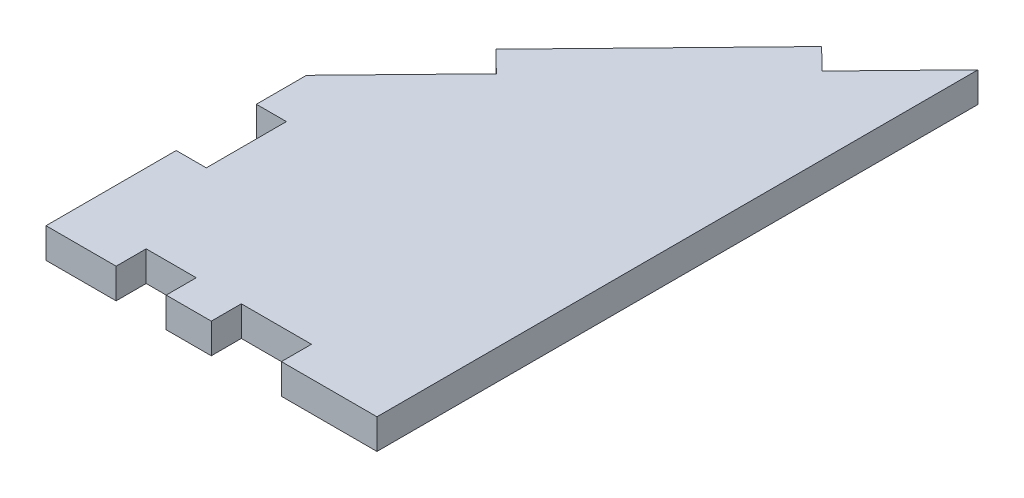
SolidWorks part; units mm, degrees
material "Acrylic (Medium-high impact)"
ref_plane "Front Plane" through (0, 0, 0) normal (0, 0, 1) x (1, 0, 0)
ref_plane "Top Plane" through (0, 0, 0) normal (0, 1, 0) x (1, 0, 0)
ref_plane "Right Plane" through (0, 0, 0) normal (1, 0, 0) x (0, 0, -1)
sketch "Sketch1" plane through (0, 0, 0) normal (0, 1, 0) x (1, 0, 0)
  line L0 (1571.1716, -4116.1736) -> (1571.1716, -4111.1736)
  line L1 (1604.2116, -4077.1736) -> (1596.5456, -4085.0623)
  line L2 (1574.1716, -4124.1736) -> (1574.1716, -4116.1736)
  line L3 (1571.1716, -4137.1736) -> (1578.1716, -4137.1736)
  line L4 (1604.2116, -4077.1736) -> (1604.2116, -4137.1736)
  line L5 (1578.1716, -4137.1736) -> (1578.1716, -4134.1736)
  line L6 (1578.1716, -4134.1736) -> (1583.1716, -4134.1736)
  line L7 (1583.1716, -4134.1736) -> (1583.1716, -4137.1736)
  line L8 (1571.1716, -4124.1736) -> (1574.1716, -4124.1736)
  line L9 (1580.5166, -4101.557) -> (1571.1716, -4111.1736)
  line L10 (1574.1716, -4116.1736) -> (1571.1716, -4116.1736)
  line L11 (1571.1716, -4124.1736) -> (1571.1716, -4137.1736)
  line L12 (1587.6716, -4137.1736) -> (1587.6716, -4134.1736)
  line L13 (1587.6716, -4134.1736) -> (1594.6716, -4134.1736)
  line L14 (1594.6716, -4134.1736) -> (1594.6716, -4137.1736)
  line L15 (1594.6716, -4137.1736) -> (1604.2116, -4137.1736)
  line L16 (1580.5166, -4101.557) -> (1578.3652, -4099.4662)
  line L17 (1578.3652, -4099.4662) -> (1594.3941, -4082.9716)
  line L18 (1594.3941, -4082.9716) -> (1596.5456, -4085.0623)
  line L19 (1583.1716, -4137.1736) -> (1587.6716, -4137.1736)
  dimension "D2" = 33.04
  dimension "D4" = 8
  dimension "D5" = 3
  dimension "D6" = 5
  dimension "D7" = 11
  dimension "D8" = 23
  dimension "D9" = 16.5
  dimension "D10" = 13
  dimension "D11" = 60
  dimension "D13" = 7
  dimension "D14" = 5
  dimension "D15" = 7
extrude "Boss-Extrude1" add sketch "Sketch1" along normal blind 3
